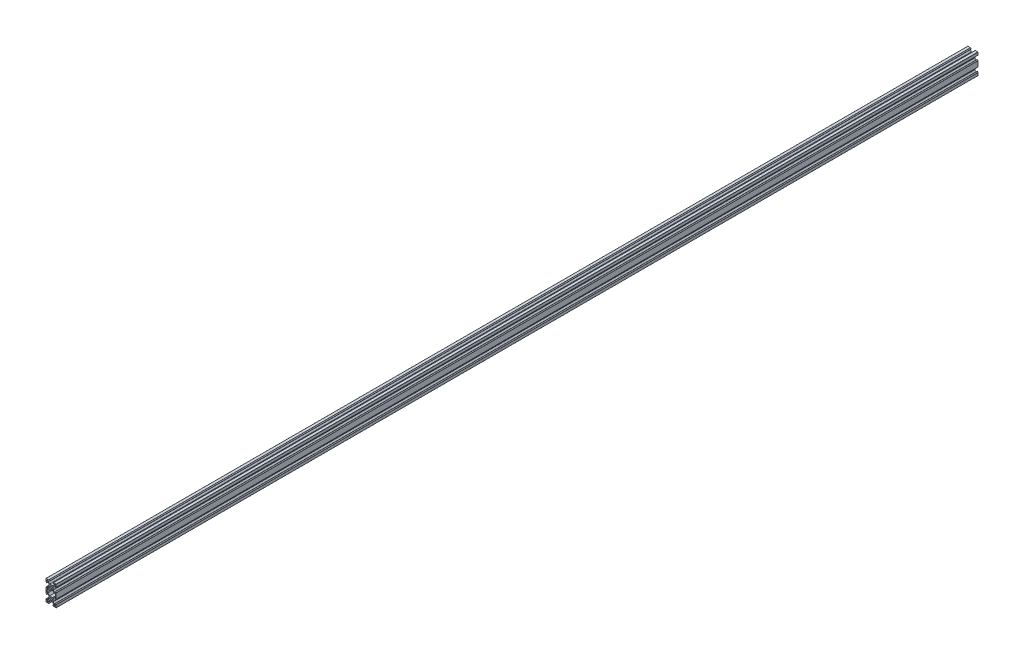
SolidWorks part; units mm, degrees
material "1060 Alloy"
ref_plane "Front Plane" through (0, 0, 0) normal (0, 0, 1) x (1, 0, 0)
ref_plane "Top Plane" through (0, 0, 0) normal (0, 1, 0) x (1, 0, 0)
ref_plane "Right Plane" through (0, 0, 0) normal (1, 0, 0) x (0, 0, -1)
sketch "Sketch1" plane through (0, 0, 0) normal (0, 0, 1) x (1, 0, 0)
  line L0 (8.2, -10) -> (10, -10)
  line L2 (10, -10) -> (10, -4.64)
  line L3 (10, -4.64) -> (8.2, -2.84)
  line L4 (8.2, -2.84) -> (8.2, -5.8007)
  line L5 (8.2, -5.8007) -> (6.8613, -5.8007)
  line L6 (6.8613, -5.8007) -> (3.9007, -2.84)
  line L7 (3.9007, -2.84) -> (3.9007, 2.84)
  line L8 (3.9007, 2.84) -> (6.56, 5.4993)
  line L9 (6.56, 5.4993) -> (8.2, 5.4993)
  line L10 (8.2, 5.4993) -> (8.2, 2.84)
  line L11 (8.2, 2.84) -> (10, 4.64)
  line L12 (10, 4.64) -> (10, 10)
  line L13 (10, 10) -> (4.64, 10)
  line L14 (4.64, 10) -> (2.84, 8.2)
  line L15 (2.84, 8.2) -> (5.4993, 8.2)
  line L16 (5.4993, 8.2) -> (5.4993, 6.56)
  line L17 (5.4993, 6.56) -> (2.84, 3.9007)
  line L18 (2.84, 3.9007) -> (-2.84, 3.9007)
  line L19 (-2.84, 3.9007) -> (-5.4993, 6.56)
  line L20 (-5.4993, 6.56) -> (-5.4993, 8.2)
  line L21 (-5.4993, 8.2) -> (-2.84, 8.2)
  line L22 (-2.84, 8.2) -> (-4.64, 10)
  line L23 (-4.64, 10) -> (-10, 10)
  line L24 (-10, 10) -> (-10, 4.64)
  line L25 (-10, 4.64) -> (-8.2, 2.84)
  line L26 (-8.2, 2.84) -> (-8.2, 5.4993)
  line L27 (-8.2, 5.4993) -> (-6.56, 5.4993)
  line L28 (-6.56, 5.4993) -> (-3.9007, 2.84)
  line L29 (-3.9007, 2.84) -> (-3.9007, -2.84)
  line L30 (-3.9007, -2.84) -> (-6.8613, -5.8007)
  line L31 (-6.8613, -5.8007) -> (-8.2, -5.8007)
  line L32 (-8.2, -5.8007) -> (-8.2, -2.84)
  line L33 (-8.2, -2.84) -> (-10, -4.64)
  line L34 (-10, -4.64) -> (-10, -10)
  line L64 (8.2, -7.3007) -> (8.2, -10)
  line L70 (-8.2, -10) -> (-8.2, -7.3007)
  line L71 (-8.2, -7.3007) -> (-6.24, -7.3007)
  line L72 (-6.24, -7.3007) -> (-2.84, -3.9007)
  line L73 (-2.84, -3.9007) -> (2.84, -3.9007)
  line L74 (2.84, -3.9007) -> (6.24, -7.3007)
  line L75 (6.24, -7.3007) -> (8.2, -7.3007)
  line L76 (-10, -10) -> (-8.2, -10)
  circle A0 centre (0, 0) radius 2.1
  point P46 (0, -3.9007)
  point P47 (0, 3.9007)
  point P49 (-3.9007, 0)
  point P50 (3.9007, 0)
  dimension "D1" = 4.2
  dimension "D8" = 1.8
  dimension "D2" = 20
  dimension "D3" = 20
  dimension "D4" = 5.68
  dimension "D5" = 90
  dimension "D6" = 10
  dimension "D7" = 10
  dimension "D9" = 1.8
  dimension "D10" = 1.8
  dimension "D11" = 1.5
  dimension "D12" = 1.5
  dimension "D13" = 1.64
  dimension "D14" = 1.5
  dimension "D15" = 1.96
extrude "Boss-Extrude2" add sketch "Sketch1" along normal blind 1800
sketch "Sketch2" plane through (0, 0, 1800) normal (0, 0, 1) x (1, 0, 0)
  line L0 (-8.2, 2.84) -> (-8.2, 5.4993) construction
  line L1 (-5.4993, 8.2) -> (-2.84, 8.2) construction
  line L2 (-8.2, 6.5693) -> (-8.2, 8.2)
  line L3 (-8.2, 8.2) -> (-6.5693, 8.2)
  line L4 (8.2, 5.4993) -> (8.2, 2.84) construction
  line L5 (8.2, 8.2) -> (8.2, 6.5693)
  line L6 (3.9007, 2.84) -> (6.56, 5.4993) construction
  line L7 (-5.4993, 6.56) -> (-5.4993, 8.2) construction
  line L8 (6.56, 5.4993) -> (8.2, 5.4993) construction
  line L11 (6.5693, 8.2) -> (6.5693, 6.56)
  line L12 (6.5693, 8.2) -> (6.5693, 7.63)
  line L16 (6.5693, 8.2) -> (8.2, 8.2)
  line L17 (-8.2, 6.5693) -> (-6.56, 6.5693)
  line L18 (-8.2, 6.5693) -> (-7.63, 6.5693)
  line L19 (-7.63, 6.5693) -> (-6.5693, 7.63)
  line L20 (6.5693, 7.63) -> (7.63, 6.5693)
  line L22 (7.63, 6.5693) -> (8.2, 6.5693)
  line L24 (-6.5693, 7.63) -> (-6.5693, 8.2)
  dimension "D5" = 1.5
  dimension "D1" = 1.07
  dimension "D3" = 1.07
  dimension "D2" = 1.07
  dimension "D4" = 1.07
extrude "Cut-Extrude1" cut sketch "Sketch2" against normal through all
fillet "Fillet1" radius 0.25 14 edges at (8.2, 2.84, 900) (-10, 4.64, 900) (-4.64, 10, 900) (4.64, 10, 900) (-10, -4.64, 900) (-10, 10, 900) (10, -4.64, 900) (10, 10, 900) (8.2, -2.84, 900) (-8.2, -2.84, 900) (-8.2, 2.84, 900) (10, 4.64, 900) (2.84, 8.2, 900) (-2.84, 8.2, 900)
ref_plane "Plane1" through (0, -10, 0) normal (0, -1, 0) x (-1, 0, 0)
mirror "Mirror1" about plane through (0, -10, 0) normal (0, -1, 0) of "Fillet1", "Boss-Extrude2"
mirror "Mirror2" about plane through (0, -10, 0) normal (0, -1, 0) of "Cut-Extrude1"
